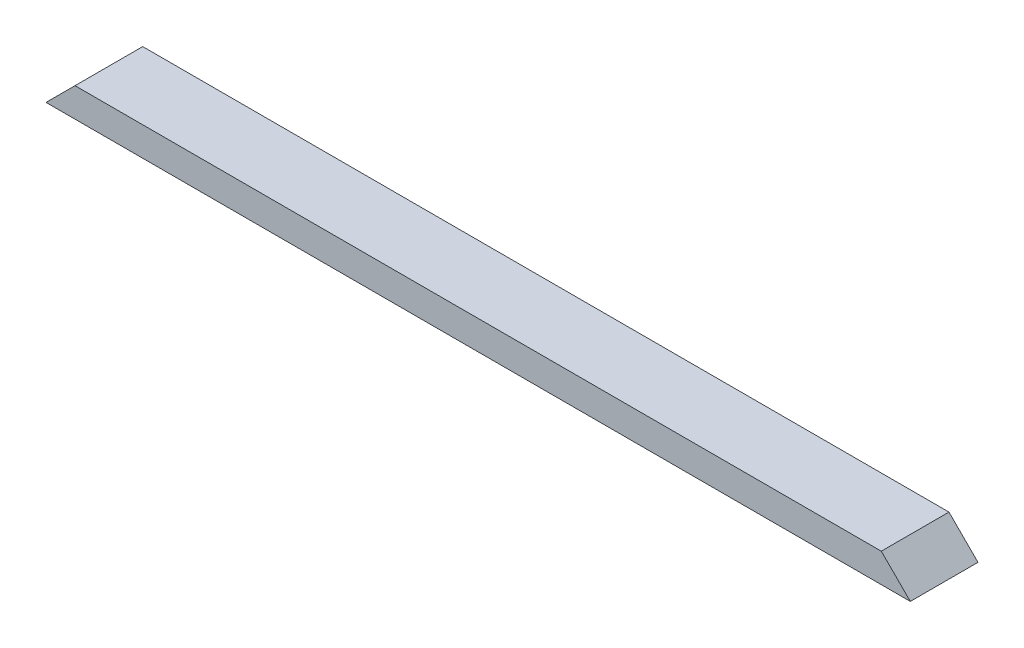
SolidWorks part; units mm, degrees
material "Pine"
ref_plane "Front Plane" through (0, 0, 0) normal (0, 0, 1) x (1, 0, 0)
ref_plane "Top Plane" through (0, 0, 0) normal (0, 1, 0) x (1, 0, 0)
ref_plane "Right Plane" through (0, 0, 0) normal (1, 0, 0) x (0, 0, -1)
sketch "Sketch1" plane through (0, 0, 0) normal (0, 1, 0) x (1, 0, 0)
  line L1 (0, 0) -> (1135.0371, 0)
  line L2 (0, 0) -> (0, 88.9)
  line L3 (0, 88.9) -> (1135.0371, 88.9)
  line L4 (1135.0371, 0) -> (1135.0371, 88.9)
  dimension "D1" = 88.9
  dimension "D2" = 1135.0371
extrude "Boss-Extrude1" add sketch "Sketch1" along normal blind 38.1
sketch "Sketch2" plane through (0, 0, 0) normal (0, 0, 1) x (1, 0, 0)
  line L0 (0, 0) -> (38.1, 38.1)
  line L1 (0, 38.1) -> (1135.0371, 38.1) construction
  line L2 (38.1, 38.1) -> (0, 38.1)
  line L3 (0, 38.1) -> (0, 0)
  line L5 (1135.0371, 0) -> (1135.0371, 38.1)
  line L9 (1135.0371, 38.1) -> (1096.9371, 38.1)
  line L10 (1096.9371, 38.1) -> (1135.0371, 0)
  dimension "D1" = 38.1
  dimension "D2" = 38.1
  dimension "D3" = 38.1
extrude "Cut-Extrude1" cut sketch "Sketch2" against normal through all
